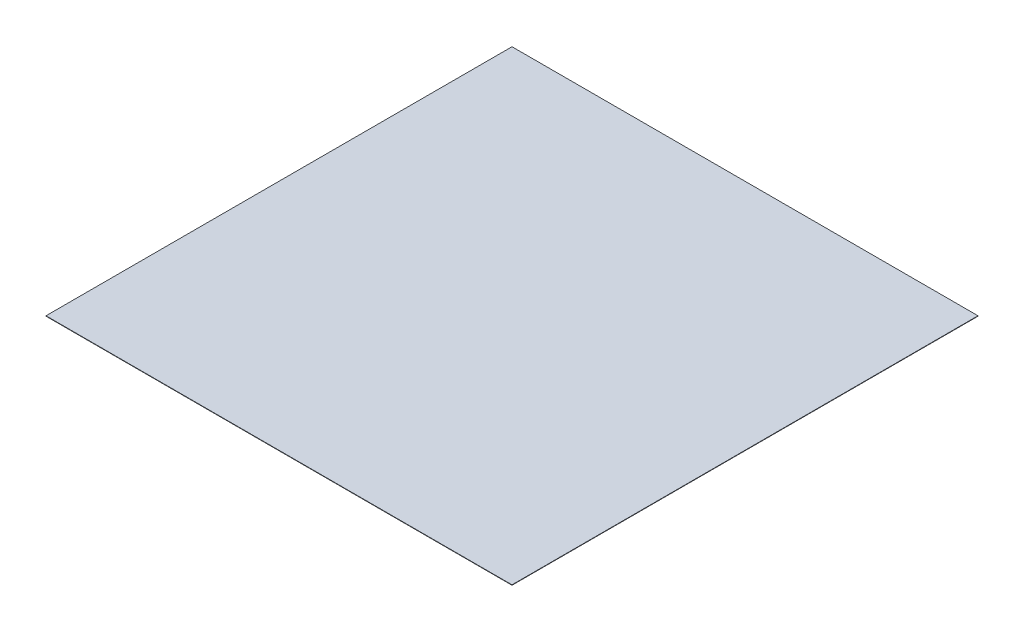
SolidWorks part; units mm, degrees
material "Nickel"
ref_plane "Plan de face" through (0, 0, 0) normal (0, 0, 1) x (1, 0, 0)
ref_plane "Plan de dessus" through (0, 0, 0) normal (0, 1, 0) x (1, 0, 0)
ref_plane "Plan de droite" through (0, 0, 0) normal (1, 0, 0) x (0, 0, -1)
sketch "Sketch1" plane through (0, 0, 0) normal (0, 1, 0) x (1, 0, 0)
  line L1 (-0.175, 0.175) -> (0.175, 0.175)
  line L2 (-0.175, 0.175) -> (-0.175, -0.175)
  line L3 (-0.175, -0.175) -> (0.175, -0.175)
  line L4 (0.175, 0.175) -> (0.175, -0.175)
  point P4 (0, 0.175)
  point P6 (-0.175, 0)
  dimension "D1" = 0.35
  dimension "D2" = 0.35
extrude "Boss-Extrude1" add sketch "Sketch1" along normal blind 0.0003
